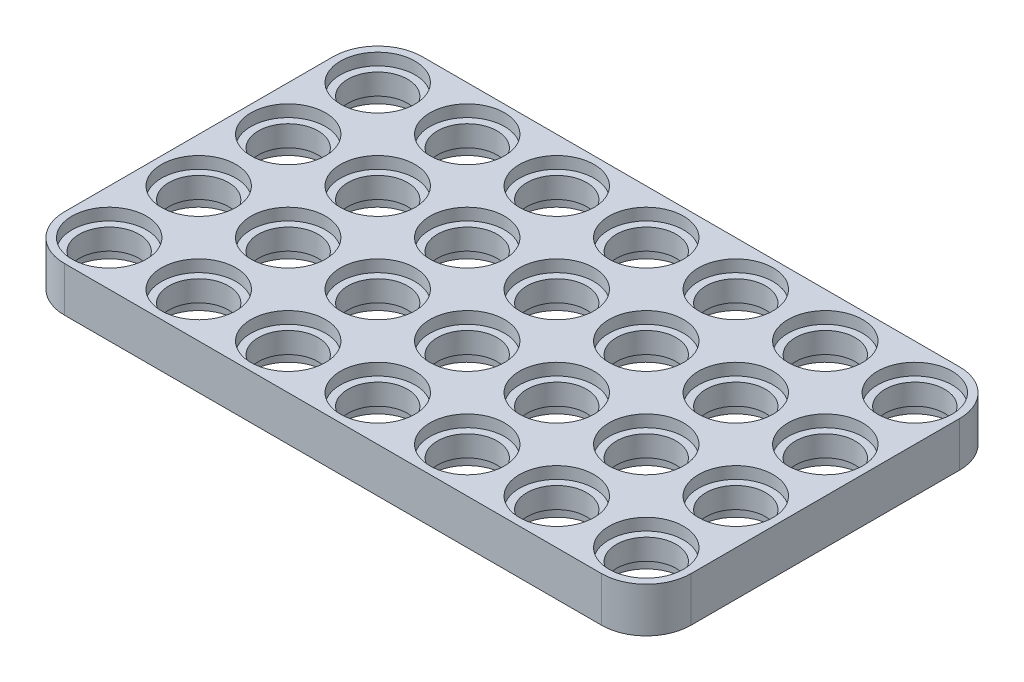
SolidWorks part; units mm, degrees
material "ABS"
ref_plane "Front Plane" through (0, 0, 0) normal (0, 0, 1) x (1, 0, 0)
ref_plane "Top Plane" through (0, 0, 0) normal (0, 1, 0) x (1, 0, 0)
ref_plane "Right Plane" through (0, 0, 0) normal (1, 0, 0) x (0, 0, -1)
sketch "Sketch1" plane through (0, 0, 0) normal (0, 1, 0) x (1, 0, 0)
  line L1 (21, -12) -> (-21, -12)
  line L2 (21, -12) -> (21, 12)
  line L3 (21, 12) -> (-21, 12)
  line L4 (-21, -12) -> (-21, 12)
  line L5 (21, -12) -> (-21, 12) construction
  line L6 (21, 12) -> (-21, -12) construction
  point P0 (0, 0)
  dimension "D1" = 42
  dimension "D2" = 24
extrude "Boss-Extrude1" add sketch "Sketch1" along normal mid plane 3
fillet "Fillet1" radius 3 4 edges at (21, 0, 12) (21, 0, -12) (-21, 0, -12) (-21, 0, 12)
sketch "Sketch2" plane through (0, 1.5, 0) normal (0, 1, 0) x (1, 0, 0)
  line L0 (18, 12) -> (-18, 12) construction
  line L1 (-21, 9) -> (-21, -9) construction
  circle A0 centre (-18, 9) radius 2
  circle A1 centre (-12, 9) radius 2
  circle A2 centre (-6, 9) radius 2
  circle A3 centre (0, 9) radius 2
  circle A4 centre (6, 9) radius 2
  circle A5 centre (12, 9) radius 2
  circle A6 centre (18, 9) radius 2
  circle A7 centre (-12, 3) radius 2
  circle A8 centre (-6, 3) radius 2
  circle A9 centre (0, 3) radius 2
  circle A10 centre (6, 3) radius 2
  circle A11 centre (12, 3) radius 2
  circle A12 centre (18, 3) radius 2
  circle A13 centre (-12, -3) radius 2
  circle A14 centre (-6, -3) radius 2
  circle A15 centre (0, -3) radius 2
  circle A16 centre (6, -3) radius 2
  circle A17 centre (12, -3) radius 2
  circle A18 centre (18, -3) radius 2
  circle A19 centre (-18, 3) radius 2
  circle A20 centre (-18, -3) radius 2
  dimension "D3" = 4
  dimension "D1" = 3
  dimension "D2" = 3
  dimension "D6" = 6
  dimension "D7" = 6
  dimension "D8" = 90
  dimension "D4" = 7
  dimension "D5" = 3
extrude "Cut-Extrude1" cut sketch "Sketch2" against normal through all
sketch "Sketch3" plane through (0, 1.5, 0) normal (0, 1, 0) x (1, 0, 0)
  circle A0 centre (-18, 9) radius 2.5
  circle A1 centre (-12, 9) radius 2.5
  circle A2 centre (-6, 9) radius 2.5
  circle A3 centre (0, 9) radius 2.5
  circle A4 centre (6, 9) radius 2.5
  circle A5 centre (12, 9) radius 2.5
  circle A6 centre (18, 9) radius 2.5
  circle A7 centre (-12, 3) radius 2.5
  circle A8 centre (-6, 3) radius 2.5
  circle A9 centre (0, 3) radius 2.5
  circle A10 centre (6, 3) radius 2.5
  circle A11 centre (12, 3) radius 2.5
  circle A12 centre (18, 3) radius 2.5
  circle A13 centre (-12, -3) radius 2.5
  circle A14 centre (-6, -3) radius 2.5
  circle A15 centre (0, -3) radius 2.5
  circle A16 centre (6, -3) radius 2.5
  circle A17 centre (12, -3) radius 2.5
  circle A18 centre (18, -3) radius 2.5
  circle A19 centre (-18, 3) radius 2.5
  circle A20 centre (-18, -3) radius 2.5
  dimension "D1" = 5
  dimension "D4" = 90
  dimension "D5" = 6
  dimension "D6" = 6
  dimension "D2" = 7
  dimension "D3" = 3
extrude "Cut-Extrude2" cut sketch "Sketch3" against normal blind 0.8
mirror "Mirror1" about plane through (0, 0, 0) normal (0, 1, 0) of "Cut-Extrude2"
mirror "Mirror2" about plane through (0, 0, 0) normal (0, 0, 1) of "Cut-Extrude1", "Mirror1", "Cut-Extrude2"
